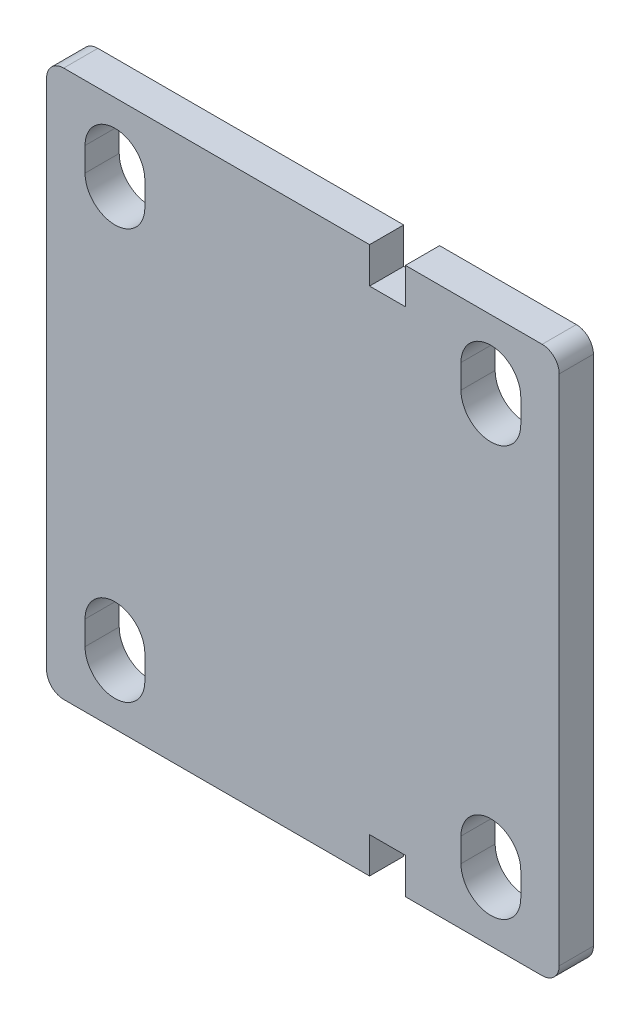
SolidWorks part; units mm, degrees
material "1.0038 (S235JRG2)"
ref_plane "Plan de face" through (0, 0, 0) normal (0, 0, 1) x (1, 0, 0)
ref_plane "Plan de dessus" through (0, 0, 0) normal (0, 1, 0) x (1, 0, 0)
ref_plane "Plan de droite" through (0, 0, 0) normal (1, 0, 0) x (0, 0, -1)
sketch "Esquisse1" plane through (0, 0, 0) normal (0, 0, 1) x (1, 0, 0)
  line L0 (0, 0) -> (150, 0)
other "Elément mécano-soudé1"
ref_plane "Plan1" through (0, 0, 0) normal (1, 0, 0) x (0, 1, 0)
sketch "plat" plane through (0, 0, 0) normal (1, 0, 0) x (0, 1, 0)
  line L0 (-80, 0) -> (80, 0) construction
  line L1 (-80, 5) -> (80, 5)
  line L2 (-80, 5) -> (-80, -5)
  line L3 (-80, -5) -> (80, -5)
  line L4 (80, 5) -> (80, -5)
  line L5 (0, 5) -> (0, -5) construction
  point P8 (0, 0)
  dimension "B" = 160
  dimension "A" = 10
hole_wizard "Dégagement M161" positions "Esquisse3" profile "Esquisse2" hole size "M16" standard "ISO"
sketch "Esquisse3" plane through (0, 0, 5) normal (0, 0, 1) x (1, 0, 0)
  line L0 (150, 80) -> (150, -80) construction
  line L1 (150, -80) -> (0, -80) construction
  line L2 (130, -60) -> (130, 60) construction
  line L3 (130, 60) -> (20, 60) construction
  line L4 (20, 60) -> (20, -60) construction
  line L5 (20, -60) -> (130, -60) construction
  line L7 (0, 80) -> (0, -80) construction
  point P0 (130, -60)
  point P1 (130, 60)
  point P3 (20, 60)
  point P5 (20, -60)
  dimension "D1" = 20
  dimension "D2" = 20
  dimension "D3" = 120
  dimension "D4" = 20
sketch "Esquisse2" plane through (130, -60, 5) normal (1, 0, 0) x (0, -1, 0)
  line L0 (0, 0) -> (0, 15.2575)
  line L1 (0, 15.2575) -> (8.75, 10)
  line L2 (8.75, 10) -> (8.75, 0)
  line L5 (8.75, 0) -> (0, 0)
  line L10 (0, 15.2575) -> (-8.75, 10) construction
  line L11 (0, -6.35) -> (0, 107.95) construction
  dimension "Diamètre du perçage" = 17.5
  dimension "Profondeur du perçage" = 10
  dimension "Angle de pointe" = 118
sketch "Esquisse4" plane through (0, 0, 5) normal (0, 0, 1) x (1, 0, 0)
  line L0 (150, 80) -> (0, 80) construction
  line L1 (94.5, 80) -> (105, 80)
  line L2 (94.5, 80) -> (94.5, 69.5)
  line L3 (94.5, 69.5) -> (105, 69.5)
  line L4 (105, 80) -> (105, 69.5)
  line L5 (150, -80) -> (0, -80) construction
  line L6 (94.5, -80) -> (105, -80)
  line L7 (94.5, -80) -> (94.5, -69.5)
  line L8 (94.5, -69.5) -> (105, -69.5)
  line L9 (105, -80) -> (105, -69.5)
  line L11 (150, 80) -> (150, -80) construction
  dimension "D1" = 10.5
  dimension "D2" = 45
extrude "Enlèv. mat.-Extru.1" cut sketch "Esquisse4" against normal through all
fillet "Congé1" radius 5 4 edges at (0, 80, 0) (0, -80, 0) (150, -80, 0) (150, 80, 0)
sketch "Esquisse5" plane through (0, 0, 5) normal (0, 0, 1) x (1, 0, 0)
  line L0 (20, 56.5) -> (20, 63.5) construction
  line L1 (20, 60) -> (130, 60) construction
  line L2 (20, 60) -> (20, -60) construction
  line L3 (20, -60) -> (130, -60) construction
  line L4 (130, 60) -> (130, -60) construction
  line L5 (11.25, 56.5) -> (11.25, 63.5)
  line L6 (28.75, 56.5) -> (28.75, 63.5)
  line L7 (75, 60) -> (75, -60) construction
  line L8 (20, 0) -> (130, 0) construction
  line L9 (130, 56.5) -> (130, 63.5) construction
  line L10 (138.75, 56.5) -> (138.75, 63.5)
  line L11 (121.25, 56.5) -> (121.25, 63.5)
  line L12 (130, -56.5) -> (130, -63.5) construction
  line L13 (138.75, -56.5) -> (138.75, -63.5)
  line L14 (121.25, -56.5) -> (121.25, -63.5)
  line L15 (20, -56.5) -> (20, -63.5) construction
  line L16 (11.25, -56.5) -> (11.25, -63.5)
  line L17 (28.75, -56.5) -> (28.75, -63.5)
  arc A0 (11.25, 56.5) -> (28.75, 56.5) centre (20, 56.5) ccw
  arc A1 (28.75, 63.5) -> (11.25, 63.5) centre (20, 63.5) ccw
  circle A2 centre (20, 60) radius 8.75 construction
  arc A3 (138.75, 56.5) -> (121.25, 56.5) centre (130, 56.5) cw
  arc A4 (121.25, 63.5) -> (138.75, 63.5) centre (130, 63.5) cw
  arc A5 (138.75, -56.5) -> (121.25, -56.5) centre (130, -56.5) ccw
  arc A6 (121.25, -63.5) -> (138.75, -63.5) centre (130, -63.5) ccw
  arc A7 (11.25, -56.5) -> (28.75, -56.5) centre (20, -56.5) cw
  arc A8 (28.75, -63.5) -> (11.25, -63.5) centre (20, -63.5) cw
  point P8 (20, 60)
  point P21 (130, 60)
  point P28 (130, -60)
  point P35 (20, -60)
  dimension "D1" = 7
extrude "Enlèv. mat.-Extru.2" cut sketch "Esquisse5" against normal blind 10
